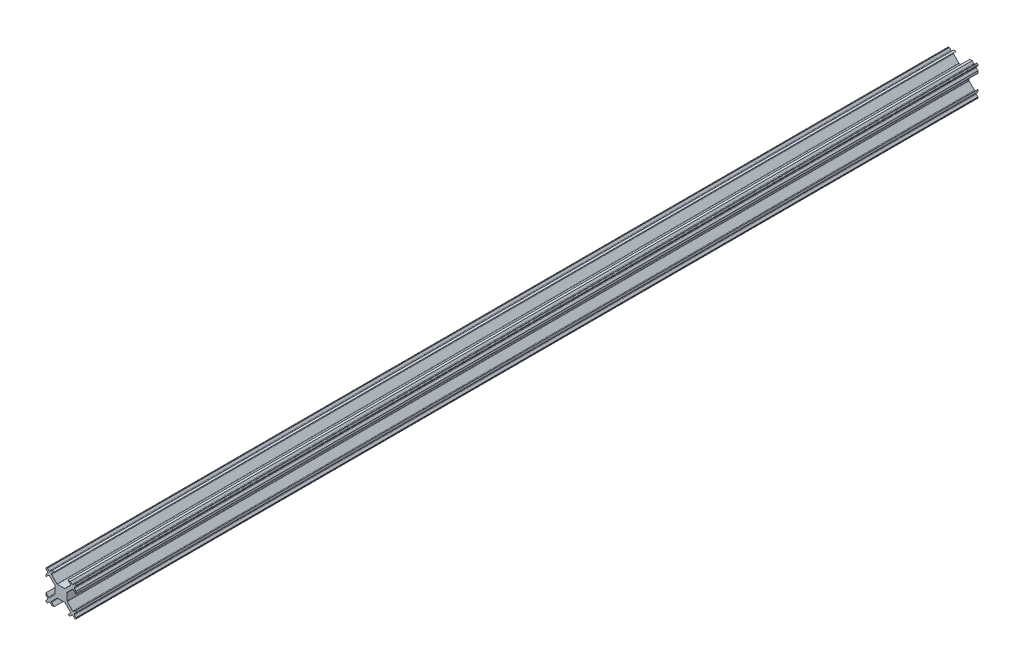
SolidWorks part; units mm, degrees
material "6063-T6"
ref_plane "Front Plane" through (0, 0, 0) normal (0, 0, 1) x (1, 0, 0)
ref_plane "Top Plane" through (0, 0, 0) normal (0, 1, 0) x (1, 0, 0)
ref_plane "Right Plane" through (0, 0, 0) normal (1, 0, 0) x (0, 0, -1)
ref_plane "Plane1" through (0, 0, 12.5) normal (0, 0, 1) x (1, 0, 0)
sketch "Sketch1" plane through (0, 0, 12.5) normal (0, 0, 1) x (1, 0, 0)
  line L0 (1.1893, 2) -> (-1.1893, 2)
  line L1 (-1.3661, 2.0732) -> (-3.1161, 3.8232)
  line L2 (-3.1161, 4.1768) -> (-2.2929, 5)
  line L3 (-2.2929, 5) -> (-3.095, 5)
  line L4 (-3.095, 5) -> (-3.6232, 4.4718)
  line L5 (-3.9768, 4.4718) -> (-4.505, 5)
  line L6 (-4.505, 5) -> (-4.75, 5)
  line L7 (-5, 4.75) -> (-5, 4.505)
  line L8 (-5, 4.505) -> (-4.4718, 3.9768)
  line L9 (-4.4718, 3.6232) -> (-5, 3.095)
  line L10 (-5, 3.095) -> (-5, 2.2929)
  line L11 (-5, 2.2929) -> (-4.1768, 3.1161)
  line L12 (-3.8232, 3.1161) -> (-2.0732, 1.3661)
  line L13 (-2, 1.1893) -> (-2, -1.1893)
  line L14 (-2.0732, -1.3661) -> (-3.8232, -3.1161)
  line L15 (-4.1768, -3.1161) -> (-5, -2.2929)
  line L16 (-5, -2.2929) -> (-5, -3.095)
  line L17 (-5, -3.095) -> (-4.4718, -3.6232)
  line L18 (-4.4718, -3.9768) -> (-5, -4.505)
  line L19 (-5, -4.505) -> (-5, -4.75)
  line L20 (-4.75, -5) -> (-4.505, -5)
  line L21 (-4.505, -5) -> (-3.9768, -4.4718)
  line L22 (-3.6232, -4.4718) -> (-3.095, -5)
  line L23 (-3.095, -5) -> (-2.2929, -5)
  line L24 (-2.2929, -5) -> (-3.1161, -4.1768)
  line L25 (-3.1161, -3.8232) -> (-1.3661, -2.0732)
  line L26 (-1.1893, -2) -> (1.1893, -2)
  line L27 (1.3661, -2.0732) -> (3.1161, -3.8232)
  line L28 (3.1161, -4.1768) -> (2.2929, -5)
  line L29 (2.2929, -5) -> (3.095, -5)
  line L30 (3.095, -5) -> (3.6232, -4.4718)
  line L31 (3.9768, -4.4718) -> (4.505, -5)
  line L32 (4.505, -5) -> (4.75, -5)
  line L33 (5, -4.75) -> (5, -4.505)
  line L34 (5, -4.505) -> (4.4718, -3.9768)
  line L35 (4.4718, -3.6232) -> (5, -3.095)
  line L36 (5, -3.095) -> (5, -2.2929)
  line L37 (5, -2.2929) -> (4.1768, -3.1161)
  line L38 (3.8232, -3.1161) -> (2.0732, -1.3661)
  line L39 (2, -1.1893) -> (2, 1.1893)
  line L40 (2.0732, 1.3661) -> (3.8232, 3.1161)
  line L41 (4.1768, 3.1161) -> (5, 2.2929)
  line L42 (5, 2.2929) -> (5, 3.095)
  line L43 (5, 3.095) -> (4.4718, 3.6232)
  line L44 (4.4718, 3.9768) -> (5, 4.505)
  line L45 (5, 4.505) -> (5, 4.75)
  line L46 (4.75, 5) -> (4.505, 5)
  line L47 (4.505, 5) -> (3.9768, 4.4718)
  line L48 (3.6232, 4.4718) -> (3.095, 5)
  line L49 (3.095, 5) -> (2.2929, 5)
  line L50 (2.2929, 5) -> (3.1161, 4.1768)
  line L51 (3.1161, 3.8232) -> (1.3661, 2.0732)
  arc A0 (1.3661, 2.0732) -> (1.1893, 2) centre (1.1893, 2.25) cw
  arc A1 (-1.1893, 2) -> (-1.3661, 2.0732) centre (-1.1893, 2.25) cw
  arc A2 (-3.1161, 3.8232) -> (-3.1161, 4.1768) centre (-2.9393, 4) cw
  arc A3 (-3.6232, 4.4718) -> (-3.9768, 4.4718) centre (-3.8, 4.6485) cw
  arc A4 (-4.75, 5) -> (-5, 4.75) centre (-4.75, 4.75) ccw
  arc A5 (-4.4718, 3.9768) -> (-4.4718, 3.6232) centre (-4.6485, 3.8) cw
  arc A6 (-4.1768, 3.1161) -> (-3.8232, 3.1161) centre (-4, 2.9393) cw
  arc A7 (-2.0732, 1.3661) -> (-2, 1.1893) centre (-2.25, 1.1893) cw
  arc A8 (-2, -1.1893) -> (-2.0732, -1.3661) centre (-2.25, -1.1893) cw
  arc A9 (-3.8232, -3.1161) -> (-4.1768, -3.1161) centre (-4, -2.9393) cw
  arc A10 (-4.4718, -3.6232) -> (-4.4718, -3.9768) centre (-4.6485, -3.8) cw
  arc A11 (-5, -4.75) -> (-4.75, -5) centre (-4.75, -4.75) ccw
  arc A12 (-3.9768, -4.4718) -> (-3.6232, -4.4718) centre (-3.8, -4.6485) cw
  arc A13 (-3.1161, -4.1768) -> (-3.1161, -3.8232) centre (-2.9393, -4) cw
  arc A14 (-1.3661, -2.0732) -> (-1.1893, -2) centre (-1.1893, -2.25) cw
  arc A15 (1.1893, -2) -> (1.3661, -2.0732) centre (1.1893, -2.25) cw
  arc A16 (3.1161, -3.8232) -> (3.1161, -4.1768) centre (2.9393, -4) cw
  arc A17 (3.6232, -4.4718) -> (3.9768, -4.4718) centre (3.8, -4.6485) cw
  arc A18 (4.75, -5) -> (5, -4.75) centre (4.75, -4.75) ccw
  arc A19 (4.4718, -3.9768) -> (4.4718, -3.6232) centre (4.6485, -3.8) cw
  arc A20 (4.1768, -3.1161) -> (3.8232, -3.1161) centre (4, -2.9393) cw
  arc A21 (2.0732, -1.3661) -> (2, -1.1893) centre (2.25, -1.1893) cw
  arc A22 (2, 1.1893) -> (2.0732, 1.3661) centre (2.25, 1.1893) cw
  arc A23 (3.8232, 3.1161) -> (4.1768, 3.1161) centre (4, 2.9393) cw
  arc A24 (4.4718, 3.6232) -> (4.4718, 3.9768) centre (4.6485, 3.8) cw
  arc A25 (5, 4.75) -> (4.75, 5) centre (4.75, 4.75) ccw
  arc A26 (3.9768, 4.4718) -> (3.6232, 4.4718) centre (3.8, 4.6485) cw
  arc A27 (3.1161, 4.1768) -> (3.1161, 3.8232) centre (2.9393, 4) cw
extrude "Boss-Extrude1" add sketch "Sketch1" against normal blind 300
